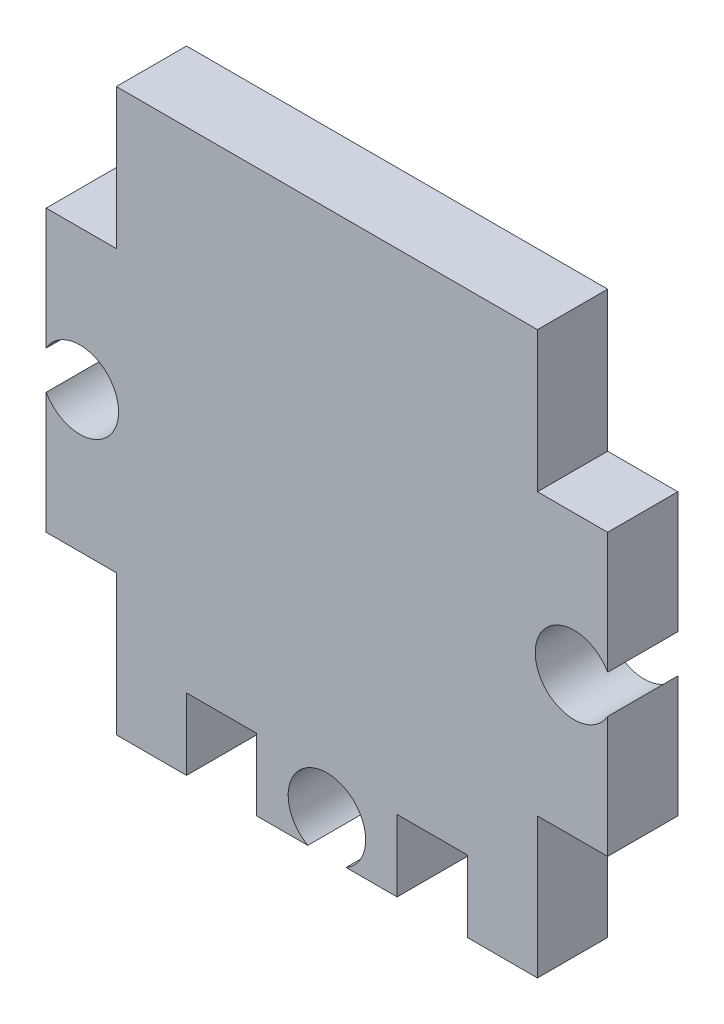
SolidWorks part; units mm, degrees
ref_plane "Front Plane" through (0, 0, 0) normal (0, 0, 1) x (1, 0, 0)
ref_plane "Top Plane" through (0, 0, 0) normal (0, 1, 0) x (1, 0, 0)
ref_plane "Right Plane" through (0, 0, 0) normal (1, 0, 0) x (0, 0, -1)
sketch "Sketch1" plane through (0, 0, 0) normal (0, 0, 1) x (1, 0, 0)
  line L0 (0, 0) -> (0, 12.7) construction
  line L1 (-9.525, 12.7) -> (9.525, 12.7)
  line L2 (-12.7, 6.35) -> (-12.7, 0.8655)
  line L3 (-9.525, -12.7) -> (-6.35, -12.7)
  line L4 (12.7, 6.35) -> (12.7, 0.8655)
  line L5 (0, 0) -> (9.4234, 0) construction
  line L6 (-12.7, 6.35) -> (-9.525, 6.35)
  line L7 (-9.525, 6.35) -> (-9.525, 12.7)
  line L8 (-9.525, -6.35) -> (-9.525, -12.7)
  line L9 (-12.7, -6.35) -> (-9.525, -6.35)
  line L10 (-12.7, -0.8655) -> (-12.7, -6.35)
  line L11 (9.525, -6.35) -> (9.525, -12.7)
  line L12 (12.7, -6.35) -> (9.525, -6.35)
  line L13 (12.7, 6.35) -> (9.525, 6.35)
  line L14 (9.525, 6.35) -> (9.525, 12.7)
  line L15 (12.7, -0.8655) -> (12.7, -6.35)
  line L16 (0.8655, -12.7) -> (3.175, -12.7)
  line L19 (-3.175, -12.7) -> (-3.175, -9.4671)
  line L20 (-3.175, -9.4671) -> (-6.35, -9.4671)
  line L21 (-6.35, -9.4671) -> (-6.35, -12.7)
  line L22 (3.175, -12.7) -> (3.175, -9.4671)
  line L23 (-3.175, -12.7) -> (-0.8655, -12.7)
  line L24 (6.35, -12.7) -> (9.525, -12.7)
  line L25 (6.35, -9.4671) -> (6.35, -12.7)
  line L26 (3.175, -9.4671) -> (6.35, -9.4671)
  arc A0 (-12.7, -0.8655) -> (-12.7, 0.8655) centre (-11.176, 0) ccw
  arc A1 (12.7, -0.8655) -> (12.7, 0.8655) centre (11.176, 0) cw
  arc A2 (0.8655, -12.7) -> (-0.8655, -12.7) centre (0, -11.176) ccw
  dimension "D6" = 3.5052
  dimension "D9" = 3.5052
  dimension "D1" = 12.7
  dimension "D2" = 12.7
  dimension "D3" = 3.175
  dimension "D4" = 6.35
  dimension "D5" = 1.524
  dimension "D7" = 6.35
  dimension "D8" = 0
  dimension "D10" = 1.524
  dimension "D11" = 3.175
  dimension "D12" = 3.175
extrude "Boss-Extrude1" add sketch "Sketch1" along normal blind 3.175
equation "\"THICK\"= 1 / 8in"
